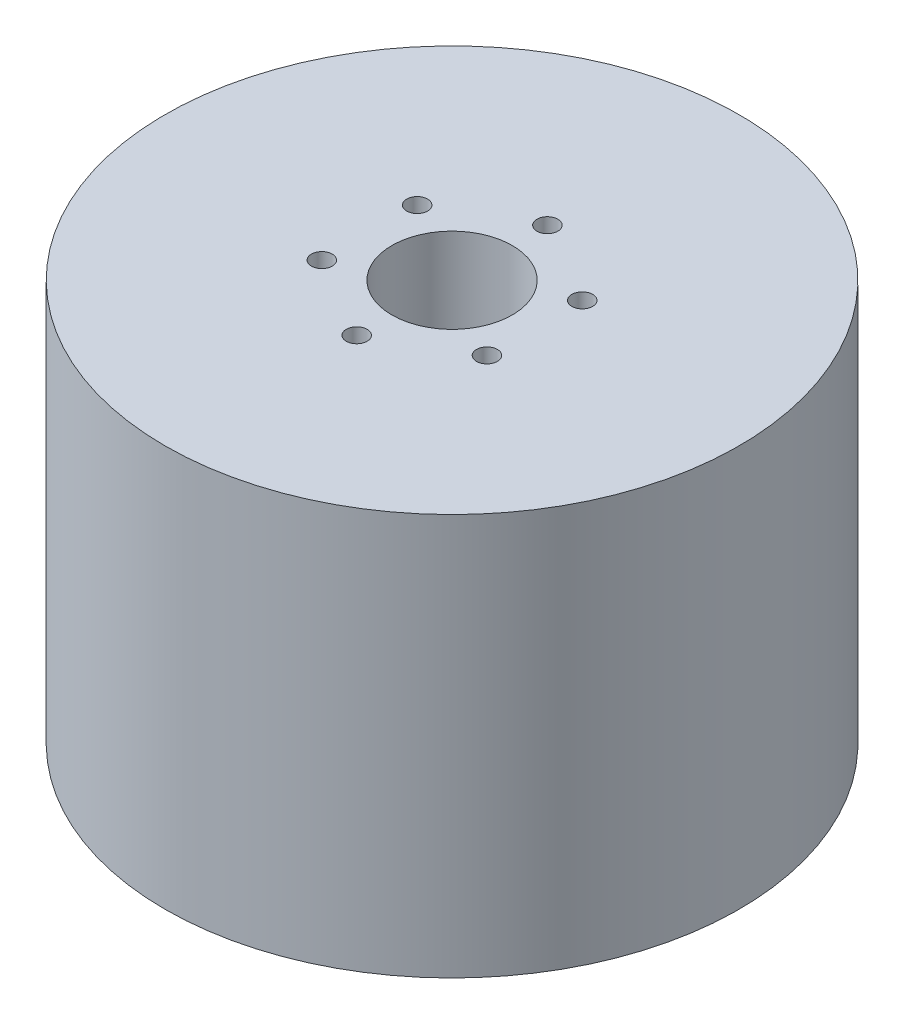
SolidWorks part; units mm, degrees
material "Nylon 101"
ref_plane "Front Plane" through (0, 0, 0) normal (0, 0, 1) x (1, 0, 0)
ref_plane "Top Plane" through (0, 0, 0) normal (0, 1, 0) x (1, 0, 0)
ref_plane "Right Plane" through (0, 0, 0) normal (1, 0, 0) x (0, 0, -1)
sketch "Sketch1" plane through (0, 0, 0) normal (0, 1, 0) x (1, 0, 0)
  circle A0 centre (0, 0) radius 71.5
  circle A1 centre (0, 0) radius 15
  circle A2 centre (0, 0) radius 23.75 construction
  circle A3 centre (0, 23.75) radius 2.6
  circle A4 centre (20.5681, 11.875) radius 2.6
  circle A5 centre (20.5681, -11.875) radius 2.6
  circle A6 centre (0, -23.75) radius 2.6
  circle A7 centre (-20.5681, -11.875) radius 2.6
  circle A8 centre (-20.5681, 11.875) radius 2.6
  point P7 (0, 0)
  point P8 (0, 0)
  point P9 (-20.5681, 11.875)
  point P20 (0, 0)
  point P21 (0, 0)
  dimension "D1" = 143
  dimension "D2" = 47.5
  dimension "D3" = 30
  dimension "D4" = 5.2
  dimension "D5" = 6
extrude "Boss-Extrude1" add sketch "Sketch1" along normal blind 100
